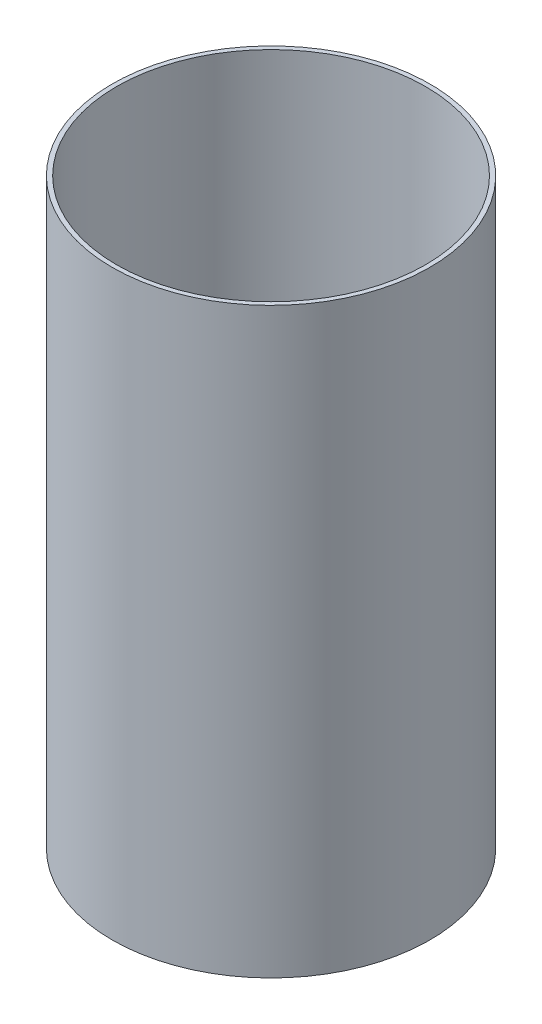
SolidWorks part; units mm, degrees
ref_plane "Front Plane" through (0, 0, 0) normal (0, 0, 1) x (1, 0, 0)
ref_plane "Top Plane" through (0, 0, 0) normal (0, 1, 0) x (1, 0, 0)
ref_plane "Right Plane" through (0, 0, 0) normal (1, 0, 0) x (0, 0, -1)
sketch "Sketch1" plane through (0, 0, 0) normal (0, 1, 0) x (1, 0, 0)
  circle A0 centre (0, 0) radius 57.15
  dimension "D1" = 114.3
extrude "Boss-Extrude1" add sketch "Sketch1" along normal blind 209.55
sketch "Sketch4" plane through (0, 0, 0) normal (0, -1, 0) x (1, 0, 0)
  circle A0 centre (0, 0) radius 55.5625
  dimension "D1" = 111.125
extrude "Cut-Extrude1" cut sketch "Sketch4" against normal through all
